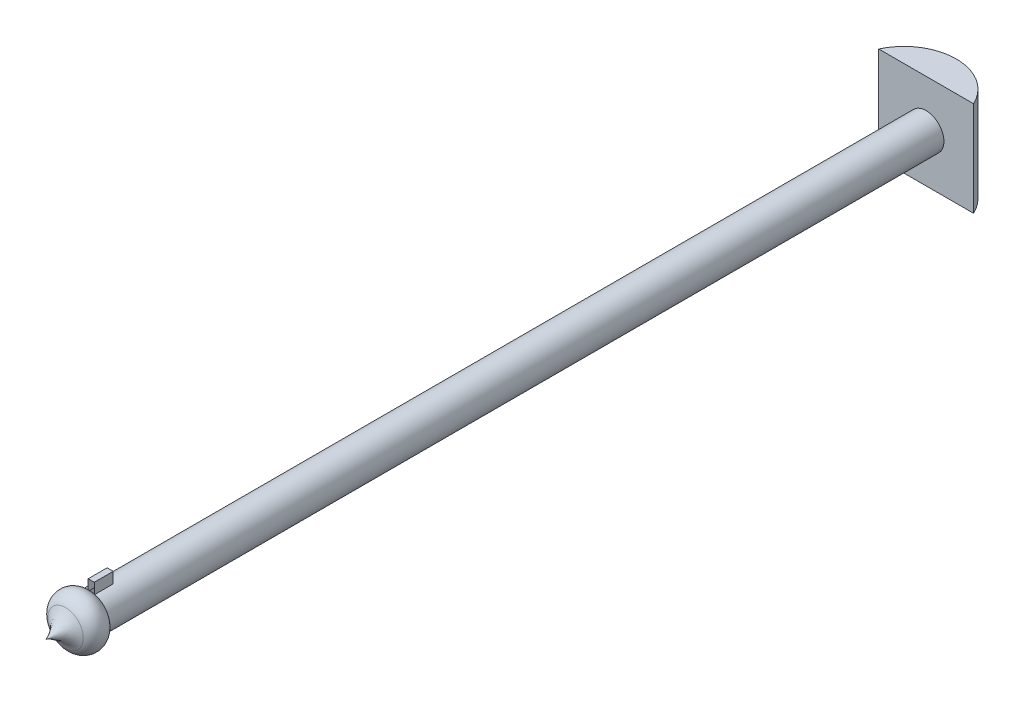
SolidWorks part; units mm, degrees
ref_plane "Front Plane" through (0, 0, 0) normal (0, 0, 1) x (1, 0, 0)
ref_plane "Top Plane" through (0, 0, 0) normal (0, 1, 0) x (1, 0, 0)
ref_plane "Right Plane" through (0, 0, 0) normal (1, 0, 0) x (0, 0, -1)
sketch "Sketch1" plane through (0, 0, 0) normal (0, 0, 1) x (1, 0, 0)
  circle A0 centre (0, 0) radius 2.3813
  dimension "D1" = 4.7625
extrude "Boss-Extrude1" add sketch "Sketch1" along normal blind 114.3
sketch "Sketch2" plane through (0, 0, 0) normal (0, 1, 0) x (1, 0, 0)
  line L0 (0, -2.5637) -> (6.35, -2.5637)
  line L1 (6.35, -2.5637) -> (-6.35, -2.5637)
  arc A0 (-6.35, -2.5637) -> (6.35, -2.5637) centre (0, -5.5378) cw
  dimension "D1" = 6.35
  dimension "D2" = 12.7
extrude "Boss-Extrude2" add sketch "Sketch2" along normal mid plane 12.7 contours A0 L1 L0
sketch "Sketch3" plane through (0, 0, 114.3) normal (0, 0, 1) x (1, 0, 0)
  line L0 (0, 0) -> (-0.3936, 0)
  line L1 (0, 0) -> (0.4208, 0)
  line L2 (0.4208, 0) -> (0.4208, 3.8007)
  line L3 (0.4208, 3.8007) -> (-0.3936, 3.8007)
  line L4 (-0.3936, 3.8007) -> (-0.3936, 0)
extrude "Boss-Extrude3" add sketch "Sketch3" against normal blind 2.54
sketch "Sketch6" plane through (0, 0, 0) normal (0, 1, 0) x (1, 0, 0)
  line L0 (-2.3813, -114.3) -> (0, -114.3)
  line L1 (0, -114.3) -> (0, -120.3378)
  arc A0 (-2.3813, -114.3) -> (-2.3708, -117.7219) centre (-1.5551, -116.0085) ccw
  arc A2 (-2.3708, -117.7219) -> (0, -120.3378) centre (-4.3658, -121.9123) cw
revolve "Revolve1" add sketch "Sketch6" angle 360 about L1
